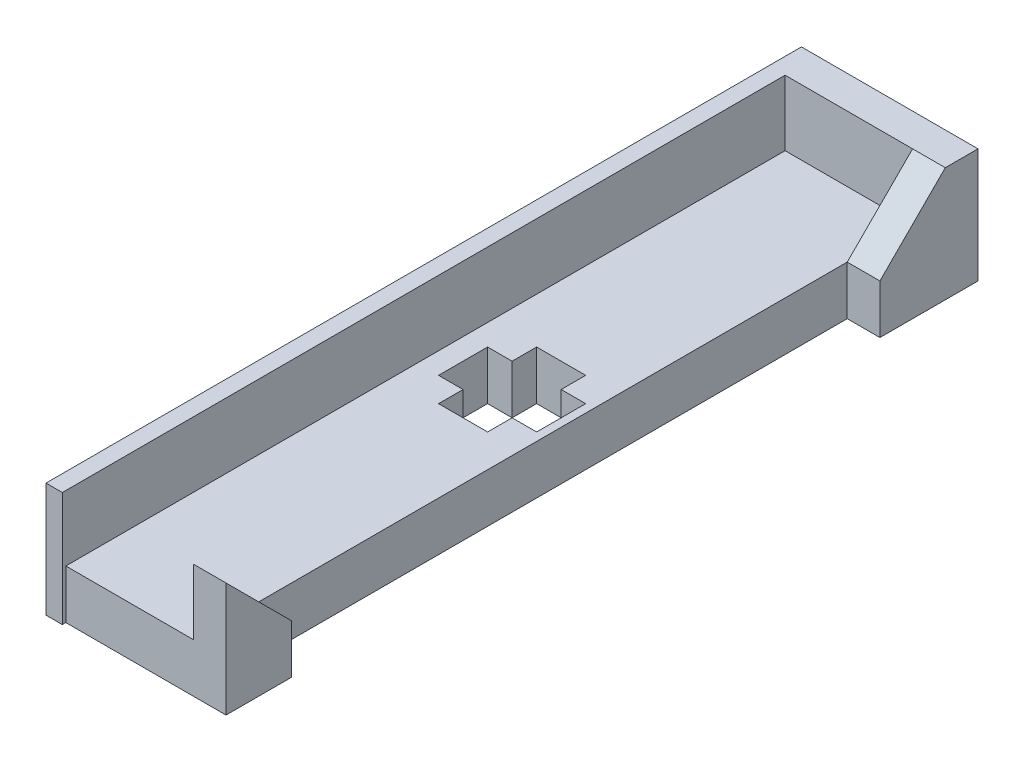
SolidWorks part; units mm, degrees
ref_plane "前视基准面" through (0, 0, 0) normal (0, 0, 1) x (1, 0, 0)
ref_plane "上视基准面" through (0, 0, 0) normal (0, 1, 0) x (1, 0, 0)
ref_plane "右视基准面" through (0, 0, 0) normal (1, 0, 0) x (0, 0, -1)
sketch "草图1" plane through (0, 0, 0) normal (0, 1, 0) x (1, 0, 0)
  line L0 (-11.5182, 0) -> (-3.7182, 0)
  line L1 (-11.5182, 0) -> (-11.5182, 44)
  line L2 (-3.7182, 0) -> (-3.7182, 44)
  line L3 (-11.5182, 44) -> (-3.7182, 44)
  point P7 (-3.523, 5.3514)
  dimension "D1" = 7.8
  dimension "D2" = 44
extrude "凸台-拉伸1" add sketch "草图1" along normal blind 3
sketch "草图2" plane through (0, 0, -44) normal (0, 0, -1) x (-1, 0, 0)
  line L0 (3.7182, 0) -> (11.5182, 0)
  line L1 (3.7182, 0) -> (3.7182, 7)
  line L2 (11.5182, 0) -> (11.5182, 7)
  line L3 (3.7182, 7) -> (11.5182, 7)
  dimension "D1" = 7
extrude "凸台-拉伸2" add sketch "草图2" along normal blind 2
sketch "草图4" plane through (-3.7182, 0, 0) normal (1, 0, 0) x (0, 0, -1)
  line L0 (46, 7) -> (44, 7)
  line L1 (44, 7) -> (40, 3)
  line L2 (0, 3) -> (44, 3) construction
  line L3 (40, 3) -> (40, 0)
  line L4 (0, 0) -> (46, 0) construction
  line L5 (40, 0) -> (46, 0)
  line L6 (46, 0) -> (46, 7)
  dimension "D1" = 4
extrude "凸台-拉伸3" add sketch "草图4" along normal blind 2
sketch "草图5" plane through (-3.7182, 0, 0) normal (1, 0, 0) x (0, 0, -1)
  line L0 (0, 0) -> (0, 7)
  line L1 (0, 7) -> (4, 3)
  line L3 (0, 3) -> (40, 3) construction
  line L5 (4, 3) -> (4, 0)
  line L6 (0, 0) -> (40, 0) construction
  line L7 (4, 0) -> (0, 0)
  dimension "D1" = 4
  dimension "D2" = 7
extrude "凸台-拉伸4" add sketch "草图5" along normal blind 2
sketch "草图6" plane through (-11.5182, 0, 0) normal (-1, 0, 0) x (0, 0, 1)
  line L0 (-46, 7) -> (-46, 0)
  line L1 (-46, 7) -> (0.2132, 7)
  line L2 (-46, 0) -> (0.2132, 0)
  line L3 (0.2132, 7) -> (0.2132, 0)
extrude "凸台-拉伸5" add sketch "草图6" along normal blind 1
sketch "草图7" plane through (0, 0, 0) normal (0, -1, 0) x (1, 0, 0)
  line L0 (-8.7182, -20) -> (-5.7182, -20)
  line L1 (-8.7182, -20) -> (-8.7182, -26)
  line L2 (-5.7182, -20) -> (-5.7182, -26)
  line L3 (-8.7182, -26) -> (-5.7182, -26)
  line L4 (-3.7182, -4) -> (-3.7182, -40) construction
  line L5 (-1.7182, -46) -> (-12.5182, -46) construction
  dimension "D1" = 3
  dimension "D2" = 6
  dimension "D3" = 2
  dimension "D4" = 20
extrude "切除-拉伸1" cut sketch "草图7" against normal blind 3
sketch "草图8" plane through (0, 0, 0) normal (0, -1, 0) x (1, 0, 0)
  line L0 (-10.2182, -21.5) -> (-4.2182, -21.5)
  line L1 (-10.2182, -21.5) -> (-10.2182, -24.5)
  line L2 (-4.2182, -21.5) -> (-4.2182, -24.5)
  line L3 (-10.2182, -24.5) -> (-4.2182, -24.5)
  line L4 (-5.7182, -26) -> (-5.7182, -20) construction
  line L5 (-8.7182, -26) -> (-5.7182, -26) construction
  dimension "D1" = 3
  dimension "D2" = 6
  dimension "D3" = 1.5
  dimension "D4" = 1.5
extrude "切除-拉伸2" cut sketch "草图8" against normal blind 3
